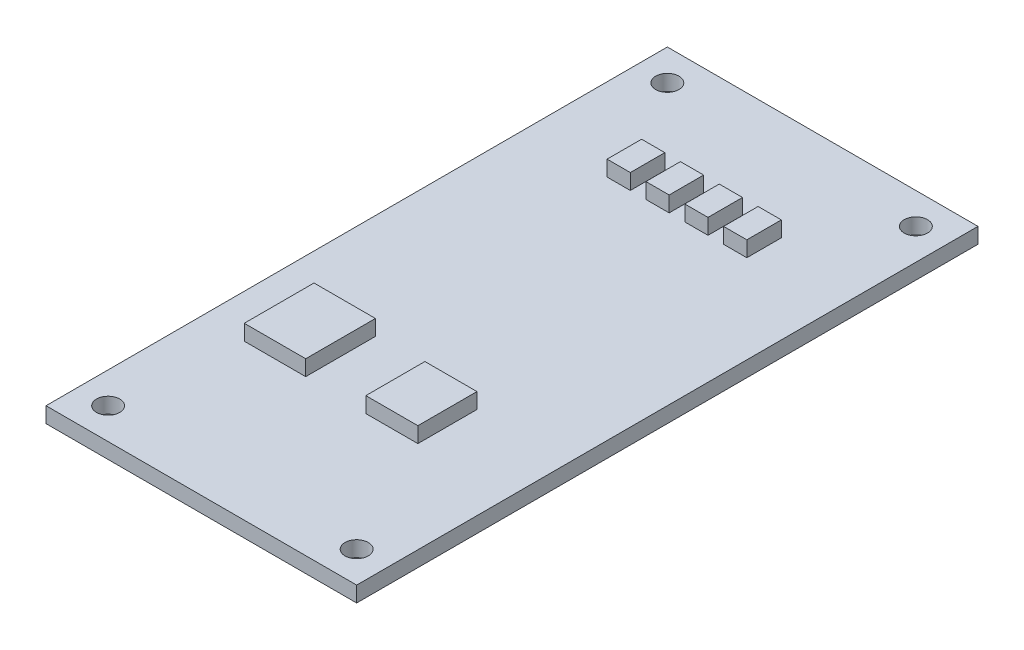
SolidWorks part; units mm, degrees
ref_plane "前视基准面" through (0, 0, 0) normal (0, 0, 1) x (1, 0, 0)
ref_plane "上视基准面" through (0, 0, 0) normal (0, 1, 0) x (1, 0, 0)
ref_plane "右视基准面" through (0, 0, 0) normal (1, 0, 0) x (0, 0, -1)
sketch "草图1" plane through (0, 0, 0) normal (0, 1, 0) x (1, 0, 0)
  line L1 (20, -40) -> (-20, -40)
  line L2 (20, -40) -> (20, 40)
  line L3 (20, 40) -> (-20, 40)
  line L4 (-20, -40) -> (-20, 40)
  line L5 (20, -40) -> (-20, 40) construction
  line L6 (20, 40) -> (-20, -40) construction
  circle A0 centre (-16, 36) radius 1.5
  circle A1 centre (16, 36) radius 1.5
  circle A2 centre (16, -36) radius 1.5
  circle A3 centre (-16, -36) radius 1.5
  point P1 (0, 0)
  dimension "D1" = 2
  dimension "D2" = 2
extrude "凸台-拉伸1" add sketch "草图1" along normal blind 2
sketch "草图2" plane through (0, 2, 0) normal (0, 1, 0) x (1, 0, 0)
  line L0 (1.4649, -12.6783) -> (8.1667, -12.6783)
  line L1 (-14.4303, -11.0632) -> (-6.5203, -11.0632)
  line L2 (-14.4303, -11.0632) -> (-14.4303, -20.042)
  line L3 (-14.4303, -20.042) -> (-6.5203, -20.042)
  line L4 (-6.5203, -11.0632) -> (-6.5203, -20.042)
  line L5 (-14.4303, -11.0632) -> (-6.5203, -20.042) construction
  line L6 (-14.4303, -20.042) -> (-6.5203, -11.0632) construction
  line L7 (1.4649, -12.6783) -> (1.4649, -20.2857)
  line L8 (1.4649, -20.2857) -> (8.1667, -20.2857)
  line L9 (8.1667, -12.6783) -> (8.1667, -20.2857)
  line L10 (1.4649, -12.6783) -> (8.1667, -20.2857) construction
  line L11 (1.4649, -20.2857) -> (8.1667, -12.6783) construction
  line L12 (-9.3741, 26.06) -> (-6.3825, 26.06)
  line L13 (-9.3741, 26.06) -> (-9.3741, 21.6175)
  line L14 (-9.3741, 21.6175) -> (-6.3825, 21.6175)
  line L15 (-6.3825, 26.06) -> (-6.3825, 21.6175)
  line L16 (-9.3741, 26.06) -> (-6.3825, 21.6175) construction
  line L17 (-9.3741, 21.6175) -> (-6.3825, 26.06) construction
  line L18 (-4.3741, 21.6175) -> (-1.3825, 21.6175)
  line L19 (-4.3741, 26.06) -> (-4.3741, 21.6175)
  line L20 (-4.3741, 26.06) -> (-1.3825, 26.06)
  line L21 (-1.3825, 26.06) -> (-1.3825, 21.6175)
  line L22 (0.6259, 21.6175) -> (3.6175, 21.6175)
  line L23 (0.6259, 26.06) -> (0.6259, 21.6175)
  line L24 (0.6259, 26.06) -> (3.6175, 26.06)
  line L25 (3.6175, 26.06) -> (3.6175, 21.6175)
  line L26 (5.6259, 21.6175) -> (8.6175, 21.6175)
  line L27 (5.6259, 26.06) -> (5.6259, 21.6175)
  line L28 (5.6259, 26.06) -> (8.6175, 26.06)
  line L29 (8.6175, 26.06) -> (8.6175, 21.6175)
  point P0 (-10.4753, -15.5526)
  point P5 (4.8158, -16.482)
  point P10 (-7.8783, 23.8388)
  dimension "D1" = 4
extrude "凸台-拉伸2" add sketch "草图2" along normal blind 2
